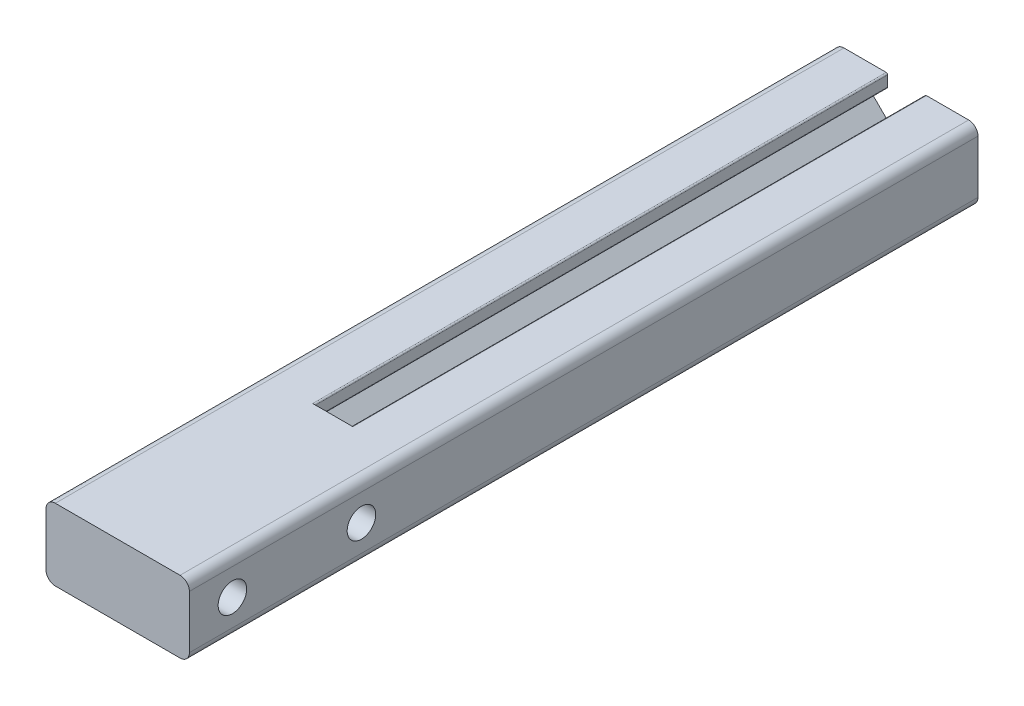
SolidWorks part; units mm, degrees
other "Imported1" parameters "D1"=101.6, "Length"=101.6
ref_plane "Front" through (0, 0, 0) normal (0, 0, 1) x (1, 0, 0)
ref_plane "Top" through (0, 0, 0) normal (0, 1, 0) x (1, 0, 0)
ref_plane "Right" through (0, 0, 0) normal (1, 0, 0) x (0, 0, -1)
sketch "Sketch1" plane through (0, 0, 0) normal (0, 0, 1) x (1, 0, 0)
  line L0 (-3.302, 12.7) -> (3.302, 12.7) construction
  line L1 (-7.493, 9.8209) -> (7.493, 9.8209) construction
  line L2 (-11.049, 12.7) -> (-3.302, 12.7)
  line L3 (3.302, 12.7) -> (11.049, 12.7)
  line L4 (11.049, 0) -> (-11.049, 0)
  line L5 (-8.509, 4.064) -> (8.509, 4.064) construction
  line L6 (-3.302, 12.7) -> (-3.302, 10.3289)
  line L7 (3.302, 12.7) -> (3.302, 10.3289)
  line L28 (-12.7, 11.049) -> (-12.7, 1.651)
  line L32 (12.7, 1.651) -> (12.7, 11.049)
  line L35 (3.302, 10.3289) -> (6.985, 10.3289)
  line L36 (7.3442, 9.4617) -> (3.4525, 5.5699)
  line L37 (1.6565, 4.826) -> (-1.6565, 4.826)
  line L38 (-3.4525, 5.5699) -> (-7.3442, 9.4617)
  line L39 (-6.985, 10.3289) -> (-3.302, 10.3289)
  circle A0 centre (-8.509, 4.064) radius 3.2385
  circle A1 centre (8.509, 4.064) radius 3.2385
  arc A36 (-12.7, 1.651) -> (-11.049, 0) centre (-11.049, 1.651) ccw
  arc A41 (11.049, 0) -> (12.7, 1.651) centre (11.049, 1.651) ccw
  arc A42 (12.7, 11.049) -> (11.049, 12.7) centre (11.049, 11.049) ccw
  arc A46 (7.3442, 9.4617) -> (6.985, 10.3289) centre (6.985, 9.8209) ccw
  arc A47 (1.6565, 4.826) -> (3.4525, 5.5699) centre (1.6565, 7.366) ccw
  arc A48 (-3.4525, 5.5699) -> (-1.6565, 4.826) centre (-1.6565, 7.366) ccw
  arc A49 (-6.985, 10.3289) -> (-7.3442, 9.4617) centre (-6.985, 9.8209) ccw
  arc A53 (-11.049, 12.7) -> (-12.7, 11.049) centre (-11.049, 11.049) ccw
  point P5 (0, 4.064)
  point P8 (0, 0)
  point P10 (0, 4.826)
  point P11 (0, 9.8209)
  point P13 (0, 12.7)
  dimension "D6" = 1.651
  dimension "D7" = 0.508
  dimension "D8" = 8.636
  dimension "D9" = 6.477
  dimension "D12" = 2.54
  dimension "D1" = 6.604
  dimension "D2" = 14.986
  dimension "D3" = 17.018
  dimension "D4" = 25.4
  dimension "D5" = 12.7
  dimension "D10" = 7.874
  dimension "D11" = 2.3711
  dimension "D13" = 45
sketch "Sketch2" plane through (0, 0, 0) normal (1, 0, 0) x (0, 0, -1)
  line L0 (50.8, 0) -> (-50.8, 0) construction
  point P4 (0, 0)
sketch "Sketch3" plane through (0, 0, 0) normal (0, 0, 1) x (1, 0, 0)
  line L0 (-11.049, 12.7) -> (-3.302, 12.7) construction
  line L1 (-3.302, 12.7) -> (-3.302, 10.3289) construction
  line L2 (-6.985, 10.3289) -> (-3.302, 10.3289) construction
  line L3 (-3.4525, 5.5699) -> (-7.3442, 9.4617) construction
  line L4 (1.6565, 4.826) -> (-1.6565, 4.826) construction
  line L5 (7.3442, 9.4617) -> (3.4525, 5.5699) construction
  line L6 (3.302, 10.3289) -> (6.985, 10.3289) construction
  line L7 (3.302, 12.7) -> (3.302, 10.3289) construction
  line L8 (3.302, 12.7) -> (11.049, 12.7) construction
  line L9 (12.7, 1.651) -> (12.7, 11.049) construction
  line L10 (11.049, 0) -> (-11.049, 0) construction
  line L11 (-12.7, 11.049) -> (-12.7, 1.651) construction
  line L12 (-11.049, 12.7) -> (-3.302, 12.7)
  line L13 (-3.302, 12.7) -> (-3.302, 10.3289)
  line L14 (-6.985, 10.3289) -> (-3.302, 10.3289)
  line L15 (-3.4525, 5.5699) -> (-7.3442, 9.4617)
  line L16 (1.6565, 4.826) -> (-1.6565, 4.826)
  line L17 (7.3442, 9.4617) -> (3.4525, 5.5699)
  line L18 (3.302, 10.3289) -> (6.985, 10.3289)
  line L19 (3.302, 12.7) -> (3.302, 10.3289)
  line L20 (3.302, 12.7) -> (11.049, 12.7)
  line L21 (12.7, 1.651) -> (12.7, 11.049)
  line L22 (11.049, 0) -> (-11.049, 0)
  line L23 (-12.7, 11.049) -> (-12.7, 1.651)
  circle A0 centre (8.509, 4.064) radius 3.2385 construction
  circle A1 centre (-8.509, 4.064) radius 3.2385 construction
  arc A2 (-6.985, 10.3289) -> (-7.3442, 9.4617) centre (-6.985, 9.8209) ccw construction
  arc A3 (-3.4525, 5.5699) -> (-1.6565, 4.826) centre (-1.6565, 7.366) ccw construction
  arc A4 (1.6565, 4.826) -> (3.4525, 5.5699) centre (1.6565, 7.366) ccw construction
  arc A5 (7.3442, 9.4617) -> (6.985, 10.3289) centre (6.985, 9.8209) ccw construction
  arc A6 (12.7, 11.049) -> (11.049, 12.7) centre (11.049, 11.049) ccw construction
  arc A7 (11.049, 0) -> (12.7, 1.651) centre (11.049, 1.651) ccw construction
  arc A8 (-12.7, 1.651) -> (-11.049, 0) centre (-11.049, 1.651) ccw construction
  arc A9 (-11.049, 12.7) -> (-12.7, 11.049) centre (-11.049, 11.049) ccw construction
  circle A10 centre (8.509, 4.064) radius 3.2385
  circle A11 centre (-8.509, 4.064) radius 3.2385
  arc A12 (-6.985, 10.3289) -> (-7.3442, 9.4617) centre (-6.985, 9.8209) ccw
  arc A13 (-3.4525, 5.5699) -> (-1.6565, 4.826) centre (-1.6565, 7.366) ccw
  arc A14 (1.6565, 4.826) -> (3.4525, 5.5699) centre (1.6565, 7.366) ccw
  arc A15 (7.3442, 9.4617) -> (6.985, 10.3289) centre (6.985, 9.8209) ccw
  arc A16 (12.7, 11.049) -> (11.049, 12.7) centre (11.049, 11.049) ccw
  arc A17 (11.049, 0) -> (12.7, 1.651) centre (11.049, 1.651) ccw
  arc A18 (-12.7, 1.651) -> (-11.049, 0) centre (-11.049, 1.651) ccw
  arc A19 (-11.049, 12.7) -> (-12.7, 11.049) centre (-11.049, 11.049) ccw
extrude "Boss-Extrude1" add sketch "Sketch3" along normal mid plane 101.6
fillet "Fillet1" radius 0.254 4 edges at (3.302, 10.3289, 0) (3.302, 12.7, 0) (-3.302, 10.3289, 0) (-3.302, 12.7, 0)
sketch "Sketch4" plane through (0, 0, 50.8) normal (0, 0, -1) x (-1, 0, 0)
  line L12 (-6.985, 10.3289) -> (-3.556, 10.3289)
  line L13 (-3.302, 10.5829) -> (-3.302, 12.446)
  line L14 (-3.556, 12.7) -> (-11.049, 12.7)
  line L15 (-12.7, 11.049) -> (-12.7, 1.651)
  line L16 (-11.049, 0) -> (11.049, 0)
  line L17 (12.7, 1.651) -> (12.7, 11.049)
  line L18 (11.049, 12.7) -> (3.556, 12.7)
  line L19 (3.302, 12.446) -> (3.302, 10.5829)
  line L20 (3.556, 10.3289) -> (6.985, 10.3289)
  line L21 (7.3442, 9.4617) -> (3.4525, 5.5699)
  line L22 (1.6565, 4.826) -> (-1.6565, 4.826)
  line L23 (-3.4525, 5.5699) -> (-7.3442, 9.4617)
  line L26 (3.556, 12.7) -> (-11.049, 12.7)
  line L27 (-12.7, 11.049) -> (-12.7, 1.651)
  line L28 (-11.049, 0) -> (11.049, 0)
  line L29 (12.7, 1.651) -> (12.7, 11.049)
  line L30 (11.049, 12.7) -> (3.556, 12.7)
  arc A12 (-3.556, 10.3289) -> (-3.302, 10.5829) centre (-3.556, 10.5829) ccw
  arc A13 (-3.302, 12.446) -> (-3.556, 12.7) centre (-3.556, 12.446) ccw
  arc A14 (-11.049, 12.7) -> (-12.7, 11.049) centre (-11.049, 11.049) ccw
  arc A15 (-12.7, 1.651) -> (-11.049, 0) centre (-11.049, 1.651) ccw
  arc A16 (11.049, 0) -> (12.7, 1.651) centre (11.049, 1.651) ccw
  arc A17 (12.7, 11.049) -> (11.049, 12.7) centre (11.049, 11.049) ccw
  arc A18 (3.556, 12.7) -> (3.302, 12.446) centre (3.556, 12.446) ccw
  arc A19 (3.302, 10.5829) -> (3.556, 10.3289) centre (3.556, 10.5829) ccw
  arc A20 (7.3442, 9.4617) -> (6.985, 10.3289) centre (6.985, 9.8209) ccw
  arc A21 (1.6565, 4.826) -> (3.4525, 5.5699) centre (1.6565, 7.366) ccw
  arc A22 (-3.4525, 5.5699) -> (-1.6565, 4.826) centre (-1.6565, 7.366) ccw
  arc A23 (-6.985, 10.3289) -> (-7.3442, 9.4617) centre (-6.985, 9.8209) ccw
  arc A26 (-11.049, 12.7) -> (-12.7, 11.049) centre (-11.049, 11.049) ccw
  arc A27 (-12.7, 1.651) -> (-11.049, 0) centre (-11.049, 1.651) ccw
  arc A28 (11.049, 0) -> (12.7, 1.651) centre (11.049, 1.651) ccw
  arc A29 (12.7, 11.049) -> (11.049, 12.7) centre (11.049, 11.049) ccw
  dimension "D1" = 0
extrude "Boss-Extrude2" add sketch "Sketch4" against normal blind 38.1
hole_wizard "#8 (0.199) Diameter Hole1" positions "Sketch5" profile "Sketch6" hole size "#8" standard "ANSI Inch" end condition through all
sketch "Sketch5" plane through (12.7, 0, 0) normal (1, 0, 0) x (0, 0, -1)
  line L0 (-88.9, 11.049) -> (-88.9, 1.651) construction
  line L1 (-88.9, 11.049) -> (-88.9, 1.651) construction
  point P0 (-81.28, 6.35)
  point P6 (0, 0)
  point P7 (-88.9, 6.35)
  dimension "D1" = 7.62
sketch "Sketch6" plane through (12.7, 6.35, 81.28) normal (0, 1, 0) x (0, 0, -1)
  line L0 (0, 0) -> (0, 25.4)
  line L1 (0, 25.4) -> (2.5273, 25.4)
  line L2 (2.5273, 25.4) -> (2.5273, 0)
  line L5 (2.5273, 0) -> (0, 0)
  line L11 (0, -6.35) -> (0, 107.95) construction
  dimension "Thru Hole Dia." = 5.0546
  dimension "Thru Hole Depth" = 25.4
pattern_linear "LPattern1" count 2 spacing 22.86 along (0, 0, -1) of "#8 (0.199) Diameter Hole1"
equation "\"D1@Boss-Extrude1\"=\"Length@Sketch2\""
